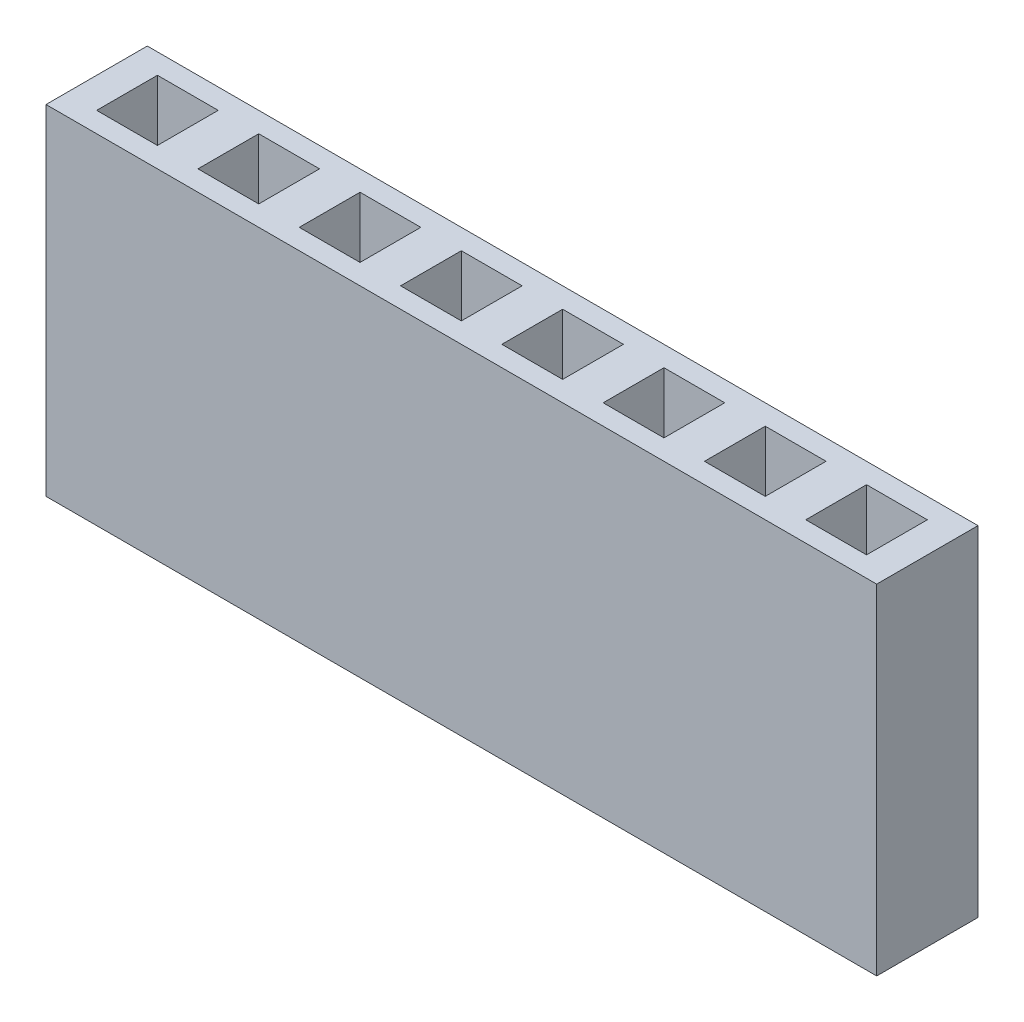
SolidWorks part; units mm, degrees
ref_plane "Front Plane" through (0, 0, 0) normal (0, 0, 1) x (1, 0, 0)
ref_plane "Top Plane" through (0, 0, 0) normal (0, 1, 0) x (1, 0, 0)
ref_plane "Right Plane" through (0, 0, 0) normal (1, 0, 0) x (0, 0, -1)
sketch "Sketch1" plane through (0, 0, 0) normal (0, 1, 0) x (1, 0, 0)
  line L1 (10.414, -1.27) -> (-10.414, -1.27)
  line L2 (10.414, -1.27) -> (10.414, 1.27)
  line L3 (10.414, 1.27) -> (-10.414, 1.27)
  line L4 (-10.414, -1.27) -> (-10.414, 1.27)
  line L5 (10.414, -1.27) -> (-10.414, 1.27) construction
  line L6 (10.414, 1.27) -> (-10.414, -1.27) construction
  point P0 (0, 0)
  dimension "D1" = 20.828
  dimension "D2" = 2.54
extrude "Boss-Extrude1" add sketch "Sketch1" along normal blind 8.509
sketch "Sketch2" plane through (0, 8.509, 0) normal (0, 1, 0) x (1, 0, 0)
  line L0 (2.032, 0.762) -> (2.032, -0.762)
  line L1 (-0.508, -0.762) -> (0.508, -0.762)
  line L2 (-0.508, -0.762) -> (-0.508, 0.762)
  line L3 (-0.508, 0.762) -> (0.508, 0.762)
  line L4 (0.508, -0.762) -> (0.508, 0.762)
  line L5 (-0.508, -0.762) -> (0.508, 0.762) construction
  line L6 (-0.508, 0.762) -> (0.508, -0.762) construction
  line L7 (-0.508, 0.762) -> (-2.032, 0.762)
  line L8 (-0.508, 0.762) -> (-0.508, -0.762)
  line L9 (-0.508, -0.762) -> (-2.032, -0.762)
  line L10 (-2.032, 0.762) -> (-2.032, -0.762)
  line L11 (2.032, 0.762) -> (0.508, 0.762)
  line L12 (0.508, 0.762) -> (0.508, -0.762)
  line L13 (2.032, -0.762) -> (0.508, -0.762)
  line L14 (4.572, 0.762) -> (4.572, -0.762)
  line L15 (4.572, 0.762) -> (3.048, 0.762)
  line L16 (3.048, 0.762) -> (3.048, -0.762)
  line L17 (4.572, -0.762) -> (3.048, -0.762)
  line L18 (7.112, 0.762) -> (7.112, -0.762)
  line L19 (7.112, 0.762) -> (5.588, 0.762)
  line L20 (5.588, 0.762) -> (5.588, -0.762)
  line L21 (7.112, -0.762) -> (5.588, -0.762)
  line L22 (9.652, 0.762) -> (9.652, -0.762)
  line L23 (9.652, 0.762) -> (8.128, 0.762)
  line L24 (8.128, 0.762) -> (8.128, -0.762)
  line L25 (9.652, -0.762) -> (8.128, -0.762)
  line L26 (-3.048, 0.762) -> (-3.048, -0.762)
  line L27 (-3.048, 0.762) -> (-4.572, 0.762)
  line L28 (-4.572, 0.762) -> (-4.572, -0.762)
  line L29 (-3.048, -0.762) -> (-4.572, -0.762)
  line L30 (-5.588, 0.762) -> (-5.588, -0.762)
  line L31 (-5.588, 0.762) -> (-7.112, 0.762)
  line L32 (-7.112, 0.762) -> (-7.112, -0.762)
  line L33 (-5.588, -0.762) -> (-7.112, -0.762)
  line L34 (-8.128, 0.762) -> (-8.128, -0.762)
  line L35 (-8.128, 0.762) -> (-9.652, 0.762)
  line L36 (-9.652, 0.762) -> (-9.652, -0.762)
  line L37 (-8.128, -0.762) -> (-9.652, -0.762)
  point P0 (0, 0)
  dimension "D1" = 1.016
  dimension "D2" = 1.524
  dimension "D3" = 1.524
  dimension "D4" = 5
  dimension "D5" = 4
extrude "Cut-Extrude1" cut sketch "Sketch2" against normal blind 5.9944 contours L7 L10 L9 L2 | L29 L26 L27 L28 | L33 L30 L31 L32 | L37 L34 L35 L36 | L13 L0 L11 L4 | L17 L14 L15 L16 | L21 L18 L19 L20 | L25 L22 L23 L24
